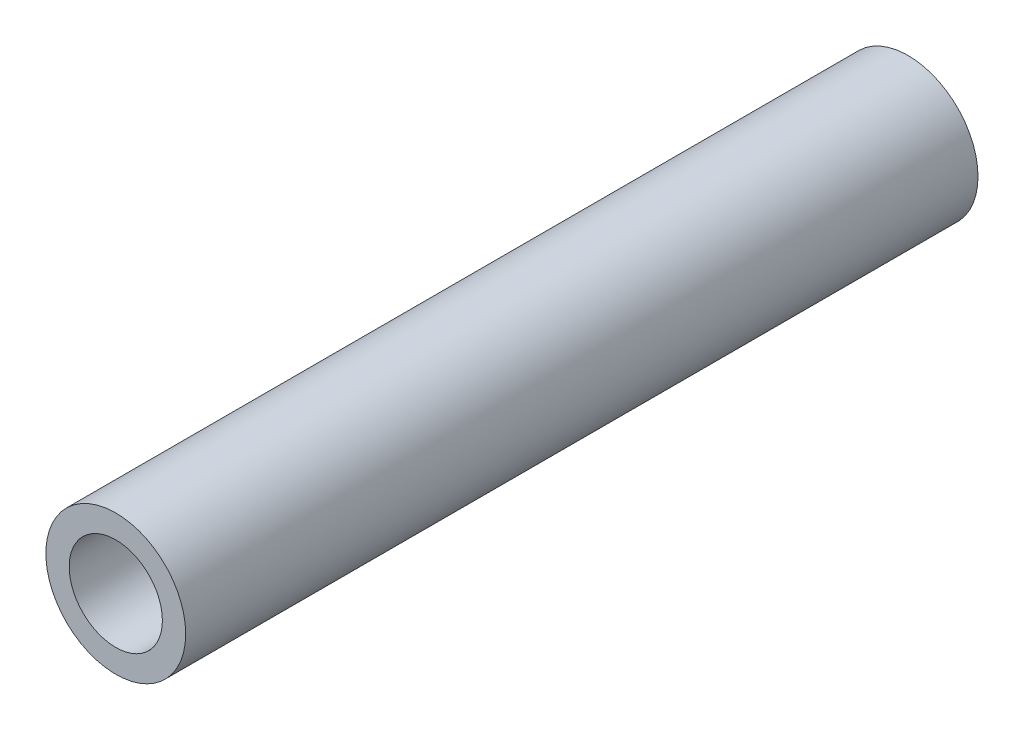
SolidWorks part; units mm, degrees
ref_plane "Plan de face" through (0, 0, 0) normal (0, 0, 1) x (1, 0, 0)
ref_plane "Plan de dessus" through (0, 0, 0) normal (0, 1, 0) x (1, 0, 0)
ref_plane "Plan de droite" through (0, 0, 0) normal (1, 0, 0) x (0, 0, -1)
sketch "Esquisse1" plane through (0, 0, 0) normal (0, 0, 1) x (1, 0, 0)
  circle A0 centre (0, 0) radius 1
  circle A1 centre (0, 0) radius 1.5
  dimension "D1" = 3
  dimension "D2" = 2
extrude "Boss.-Extru.1" add sketch "Esquisse1" along normal blind 17
